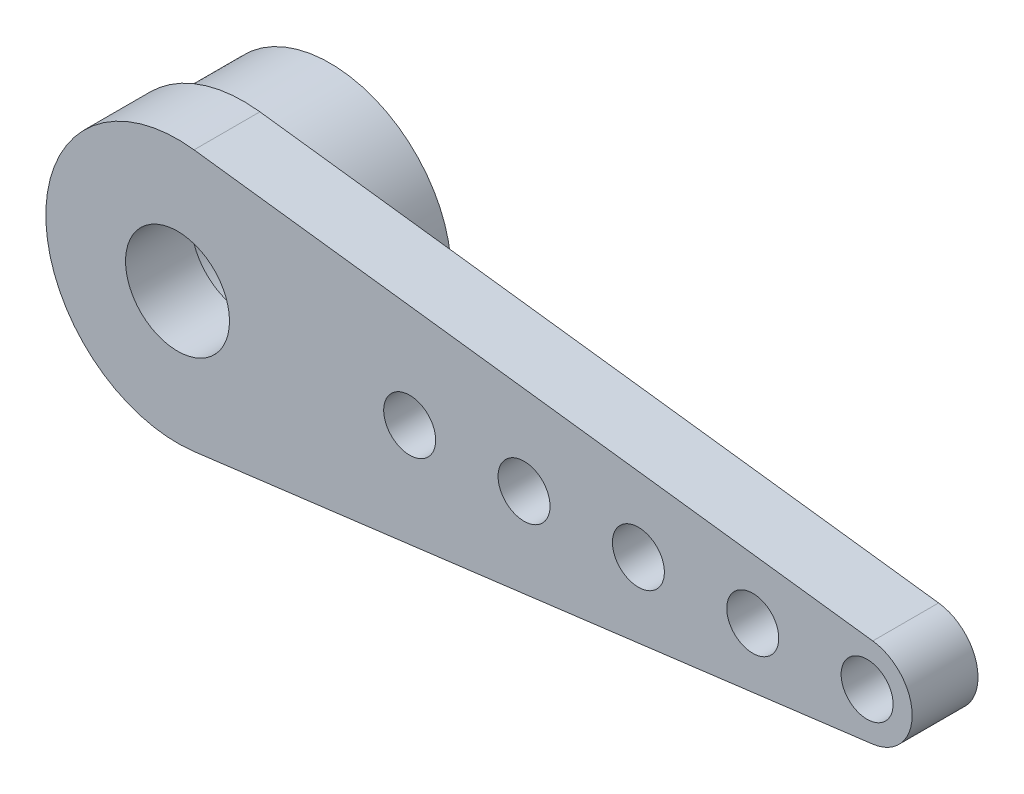
SolidWorks part; units mm, degrees
material "1.0721 (10S20)"
ref_plane "Piano frontale" through (0, 0, 0) normal (0, 0, 1) x (1, 0, 0)
ref_plane "Piano superiore" through (0, 0, 0) normal (0, 1, 0) x (1, 0, 0)
ref_plane "Piano destro" through (0, 0, 0) normal (1, 0, 0) x (0, 0, -1)
sketch "Schizzo2" plane through (0, 0, 0) normal (0, 0, 1) x (1, 0, 0)
  line L0 (-3.8, 0) -> (21.2, 0) construction
  line L1 (0.4774, 3.7699) -> (20.0633, 1.2897)
  line L2 (0.4774, -3.7699) -> (20.0633, -1.2897)
  arc A0 (0.4774, 3.7699) -> (0.4774, -3.7699) centre (0, 0) ccw
  circle A1 centre (19.9, 0) radius 0.75
  arc A3 (20.0633, -1.2897) -> (20.0633, 1.2897) centre (19.9, 0) ccw
  circle A4 centre (6.7, 0) radius 0.75
  circle A5 centre (10, 0) radius 0.75
  circle A6 centre (13.3, 0) radius 0.75
  circle A7 centre (16.6, 0) radius 0.75
  circle A8 centre (0, 0) radius 1.5
  dimension "D1" = 7.6
  dimension "D3" = 25
  dimension "D4" = 1.5
  dimension "D5" = 6.7
  dimension "D9" = 3
  dimension "D2" = 19.9
  dimension "D6" = 10
  dimension "D7" = 13.3
  dimension "D8" = 16.6
extrude "Estrusione-Estrusione1" add sketch "Schizzo2" along normal blind 1.9
sketch "Schizzo3" plane through (0, 0, 0) normal (0, 0, 1) x (1, 0, 0)
  circle A0 centre (0, 0) radius 3.5
  circle A1 centre (0, 0) radius 2.3078
  dimension "D1" = 7
extrude "Estrusione-Estrusione2" add sketch "Schizzo3" against normal blind 2.5
sketch "Schizzo4" plane through (0, 0, 0) normal (0, 0, -1) x (-1, 0, 0)
  point P0 (-19.9, 0)
